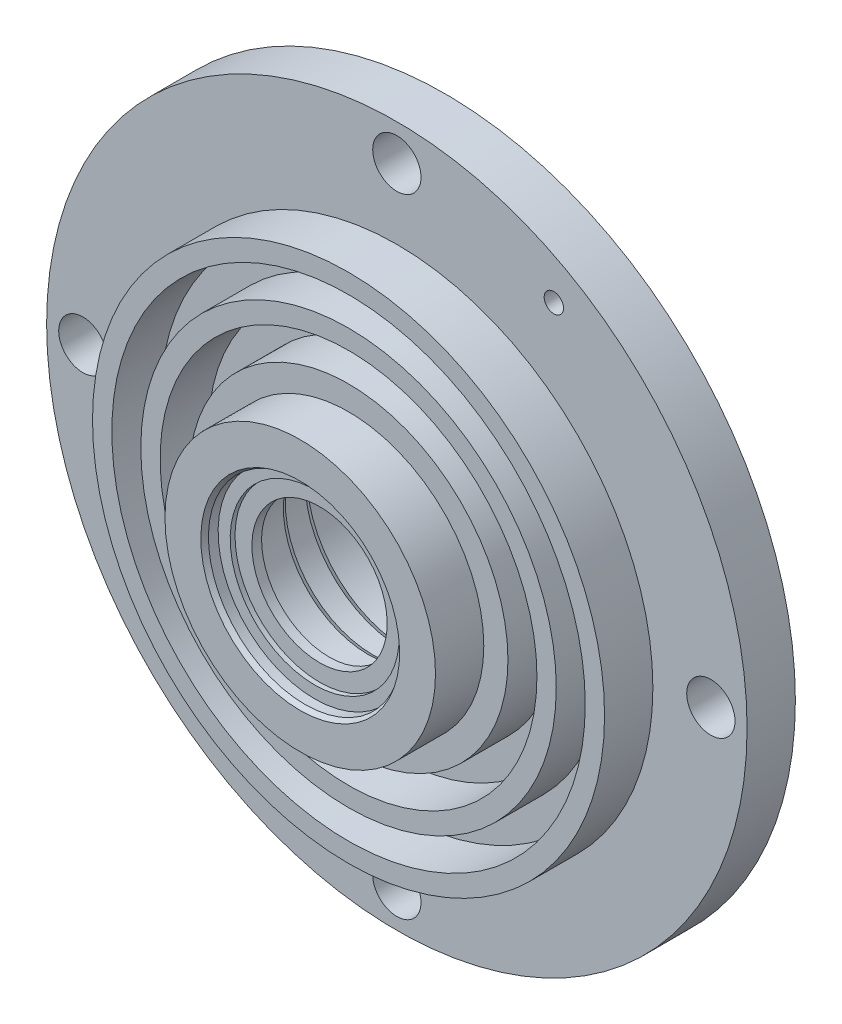
SolidWorks part; units mm, degrees
ref_plane "Plan de face" through (0, 0, 0) normal (0, 0, 1) x (1, 0, 0)
ref_plane "Plan de dessus" through (0, 0, 0) normal (0, 1, 0) x (1, 0, 0)
ref_plane "Plan de droite" through (0, 0, 0) normal (1, 0, 0) x (0, 0, -1)
sketch "Esquisse1" plane through (0, 0, 0) normal (0, 0, 1) x (1, 0, 0)
  line L0 (83.0888, 0) -> (-78.1221, 0) construction
  line L5 (0, 78.0109) -> (0, -80.6258) construction
  line L6 (32.5, 56.2917) -> (0, 0) construction
  line L7 (0, 0) -> (-32.5, -56.2917) construction
  circle A0 centre (0, 0) radius 72.5
  circle A1 centre (0, 0) radius 65 construction
  circle A2 centre (0, -65) radius 5
  circle A3 centre (65, 0) radius 5
  circle A4 centre (0, 65) radius 5
  circle A5 centre (32.5, 56.2917) radius 2
  circle A6 centre (-32.5, -56.2917) radius 2
  circle A7 centre (-65, 0) radius 5
  dimension "D5" = 130
  dimension "D9" = 65
  dimension "D19" = 4
  dimension "D20" = 4
  dimension "D3" = 145
  dimension "D4" = 10
  dimension "D6" = 30
  dimension "D7" = 30
  dimension "D18" = 65
extrude "Extrusion1" add sketch "Esquisse1" against normal blind 30
sketch "Esquisse2" plane through (0, 0, 0) normal (1, 0, 0) x (0, 0, -1)
  line L0 (0, 0) -> (55.8681, 0) construction
  line L1 (0, 0) -> (0, 18.0774) construction
  line L2 (14, 15) -> (15, 15.5774)
  line L3 (1, 17.5) -> (3, 17.5)
  line L4 (3, 17.5) -> (3, 15)
  line L5 (3, 15) -> (4, 15)
  line L6 (4, 15) -> (4, 11.5)
  line L7 (4, 11.5) -> (6, 11.5)
  line L8 (6, 11.5) -> (6, 15)
  line L9 (6, 15) -> (14, 15)
  line L12 (15, 15.5774) -> (15, 17.5)
  line L13 (15, 17.5) -> (21, 17.5)
  line L15 (30, 18.5) -> (30, 0) construction
  line L16 (22, 18.0774) -> (22, 18.5)
  line L17 (22, 18.5) -> (30, 18.5)
  line L18 (21, 17.5) -> (22, 18.0774)
  line L19 (1, 17.5) -> (0, 18.0774)
  line L20 (0, -2.5) -> (30, -2.5)
  line L21 (0, 18.0774) -> (0, -2.5)
  line L22 (30, 18.5) -> (30, -2.5)
  line L23 (0, 72.5) -> (0, -72.5) construction
  line L24 (30, -72.5) -> (30, 72.5) construction
  point P3 (22, 17.5)
  point P18 (15, 15)
  dimension "D2" = 3
  dimension "D3" = 17.5
  dimension "D4" = 1
  dimension "D5" = 14
  dimension "D6" = 17.5
  dimension "D7" = 9
  dimension "D8" = 1
  dimension "D9" = 30
  dimension "D10" = 20
  dimension "D11" = 7
  dimension "D12" = 15
  dimension "D13" = 21
  dimension "D14" = 1
  dimension "D15" = 30
  dimension "D16" = 30
  dimension "D17" = 1
  dimension "D18" = 5
  dimension "D19" = 20
revolve "Enlèvement de matière-Révolution1" cut sketch "Esquisse2" angle 360 about L20
sketch "Esquisse3" plane through (0, 0, 0) normal (1, 0, 0) x (0, 0, -1)
  line L0 (-12.602, -2.5) -> (50.7328, -2.5) construction
  line L1 (10, -41.5) -> (10, -45.5)
  line L2 (10, -35.5) -> (20, -35.5)
  line L3 (10, -35.5) -> (10, -30.5)
  line L4 (10, -41.5) -> (20, -41.5)
  line L5 (20, -35.5) -> (20, -41.5)
  line L6 (10, -51.5) -> (10, -55.5)
  line L7 (10, -45.5) -> (20, -45.5)
  line L8 (10, -30.5) -> (0, -30.5)
  line L9 (10, -51.5) -> (20, -51.5)
  line L10 (20, -45.5) -> (20, -51.5)
  line L11 (10, -55.5) -> (20, -55.5)
  line L12 (0, -30.5) -> (0, -82.5)
  line L13 (0, -82.5) -> (20, -82.5)
  line L14 (20, -55.5) -> (20, -82.5)
  line L16 (30, -72.5) -> (30, 72.5) construction
  line L17 (0, 72.5) -> (0, -72.5) construction
  line L18 (0, -72.5) -> (30, -72.5) construction
  dimension "D1" = 2.5
  dimension "D2" = 33
  dimension "D3" = 6
  dimension "D4" = 4
  dimension "D5" = 4
  dimension "D6" = 10
  dimension "D7" = 10
  dimension "D8" = 10
  dimension "D9" = 28
revolve "Enlèvement de matière-Révolution2" cut sketch "Esquisse3" angle 360 about L0
